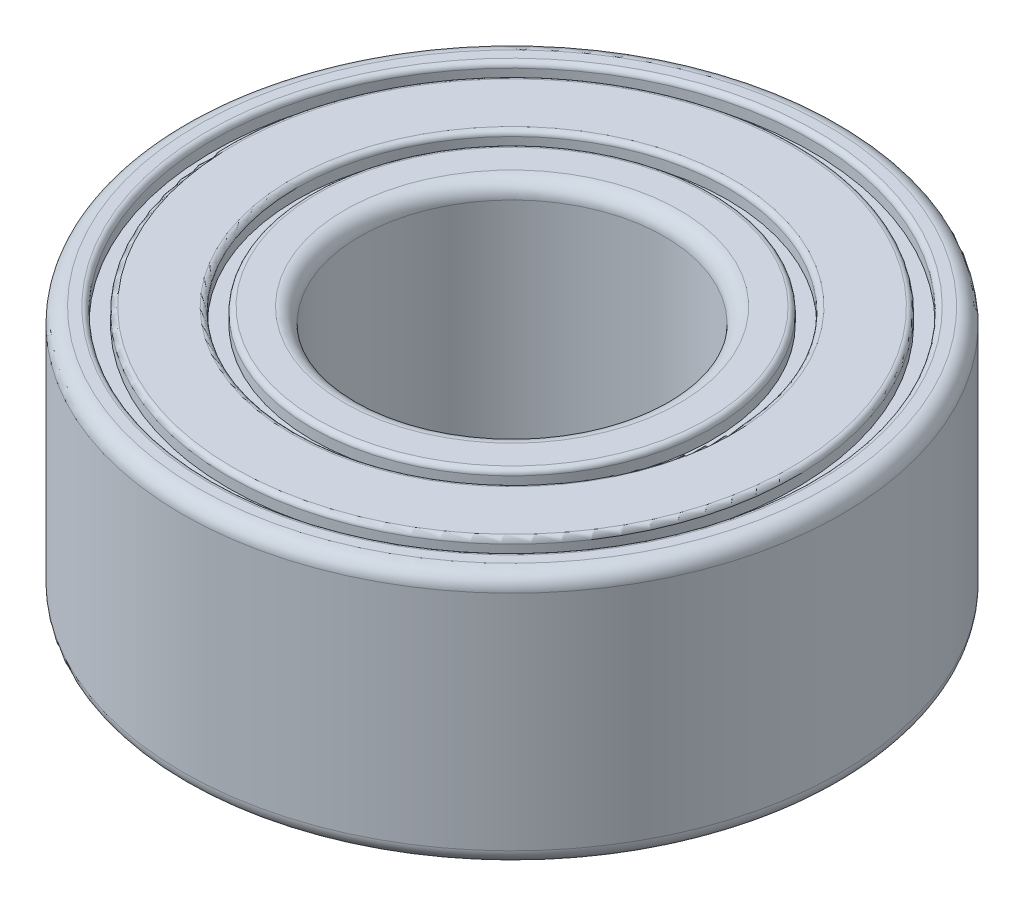
SolidWorks part; units mm, degrees
ref_plane "Front Plane" through (0, 0, 0) normal (0, 0, 1) x (1, 0, 0)
ref_plane "Top Plane" through (0, 0, 0) normal (0, 1, 0) x (1, 0, 0)
ref_plane "Right Plane" through (0, 0, 0) normal (1, 0, 0) x (0, 0, -1)
sketch "Sketch1" plane through (0, 0, 0) normal (0, 1, 0) x (1, 0, 0)
  circle A0 centre (0, 0) radius 6.5
  dimension "D1" = 13
extrude "Boss-Extrude1" add sketch "Sketch1" along normal blind 5
sketch "Sketch2" plane through (0, 5, 0) normal (0, 1, 0) x (1, 0, 0)
  circle A0 centre (0, 0) radius 3
  dimension "D1" = 6
extrude "Cut-Extrude1" cut sketch "Sketch2" against normal up to next
sketch "Sketch3" plane through (0, 5, 0) normal (0, 1, 0) x (1, 0, 0)
  circle A0 centre (0, 0) radius 3.95
  circle A1 centre (0, 0) radius 4.25
  circle A2 centre (0, 0) radius 5.6
  circle A3 centre (0, 0) radius 5.9
  dimension "D1" = 7.9
  dimension "D2" = 11.2
  dimension "D3" = 0.3
  dimension "D4" = 0.3
extrude "Cut-Extrude2" cut sketch "Sketch3" against normal blind 0.3 contours A1 A0 | A3 A2
sketch "Sketch4" plane through (0, 0, 0) normal (0, -1, 0) x (1, 0, 0)
  circle A1 centre (0, 0) radius 5.9
  circle A2 centre (0, 0) radius 5.9
  circle A3 centre (0, 0) radius 5.6
  circle A4 centre (0, 0) radius 5.6
  circle A5 centre (0, 0) radius 4.25
  circle A6 centre (0, 0) radius 4.25
  circle A7 centre (0, 0) radius 3.95
  circle A8 centre (0, 0) radius 3.95
  dimension "D1" = 0
  dimension "D2" = 0
  dimension "D3" = 0
  dimension "D4" = 0
extrude "Cut-Extrude3" cut sketch "Sketch4" against normal blind 0.3 contours A2 A4 | A6 A8
fillet "Fillet1" radius 0.1 8 edges at (0, 0, -5.6) (0, 0, -4.25) (0, 5, 5.6) (0, 5, 4.25) (0, 0, -5.9) (0, 0, -3.95) (0, 5, 3.95) (0, 5, 5.9)
fillet "Fillet2" radius 0.3 4 edges at (0, 0, 3) (0, 5, 3) (0, 0, 6.5) (0, 5, 6.5)
